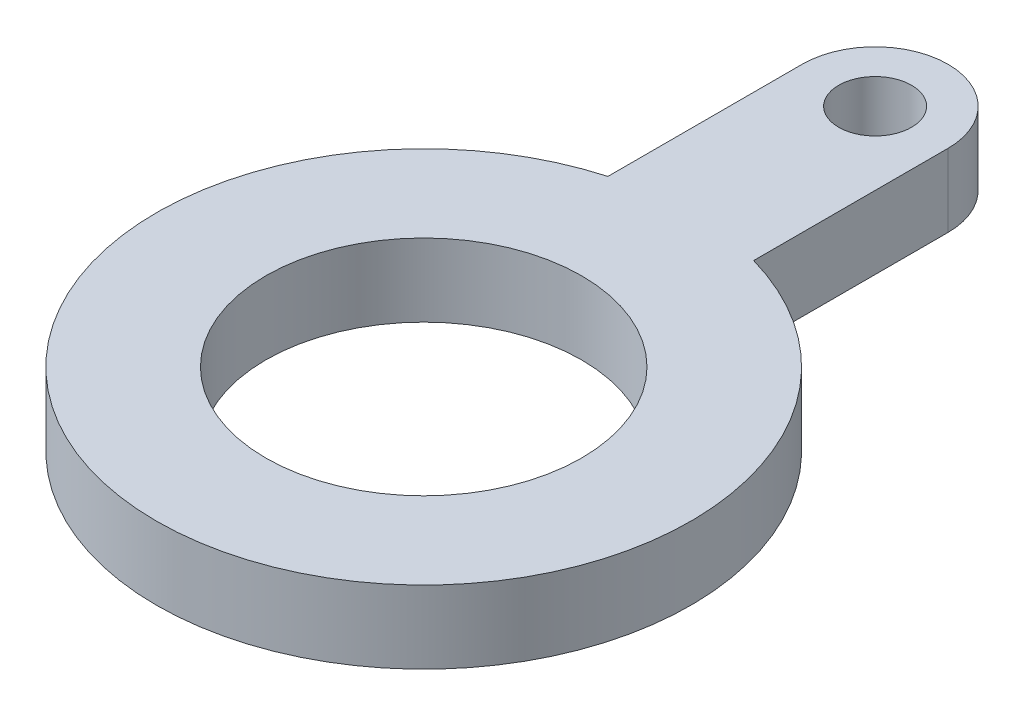
SolidWorks part; units mm, degrees
ref_plane "Front Plane" through (0, 0, 0) normal (0, 0, 1) x (1, 0, 0)
ref_plane "Top Plane" through (0, 0, 0) normal (0, 1, 0) x (1, 0, 0)
ref_plane "Right Plane" through (0, 0, 0) normal (1, 0, 0) x (0, 0, -1)
sketch "Sketch1" plane through (0, 0, 0) normal (0, 1, 0) x (1, 0, 0)
  line L0 (0, 11) -> (0, -11) construction
  line L4 (3, 10.583) -> (3, 18.583)
  line L5 (-3, 10.583) -> (-3, 18.583)
  arc A0 (-3, 10.583) -> (3, 10.583) centre (0, 0) ccw
  circle A1 centre (0, 0) radius 6.5
  arc A2 (3, 18.583) -> (-3, 18.583) centre (0, 18.583) ccw
  circle A3 centre (0, 18.583) radius 1.5
  dimension "D1" = 22
  dimension "D2" = 13
  dimension "D3" = 6
  dimension "D5" = 3
  dimension "D4" = 3
  dimension "D6" = 8
extrude "Boss-Extrude1" add sketch "Sketch1" along normal blind 3 contours L0 A1 | A1 L0 | A3 | L5 A2 L4 A0
